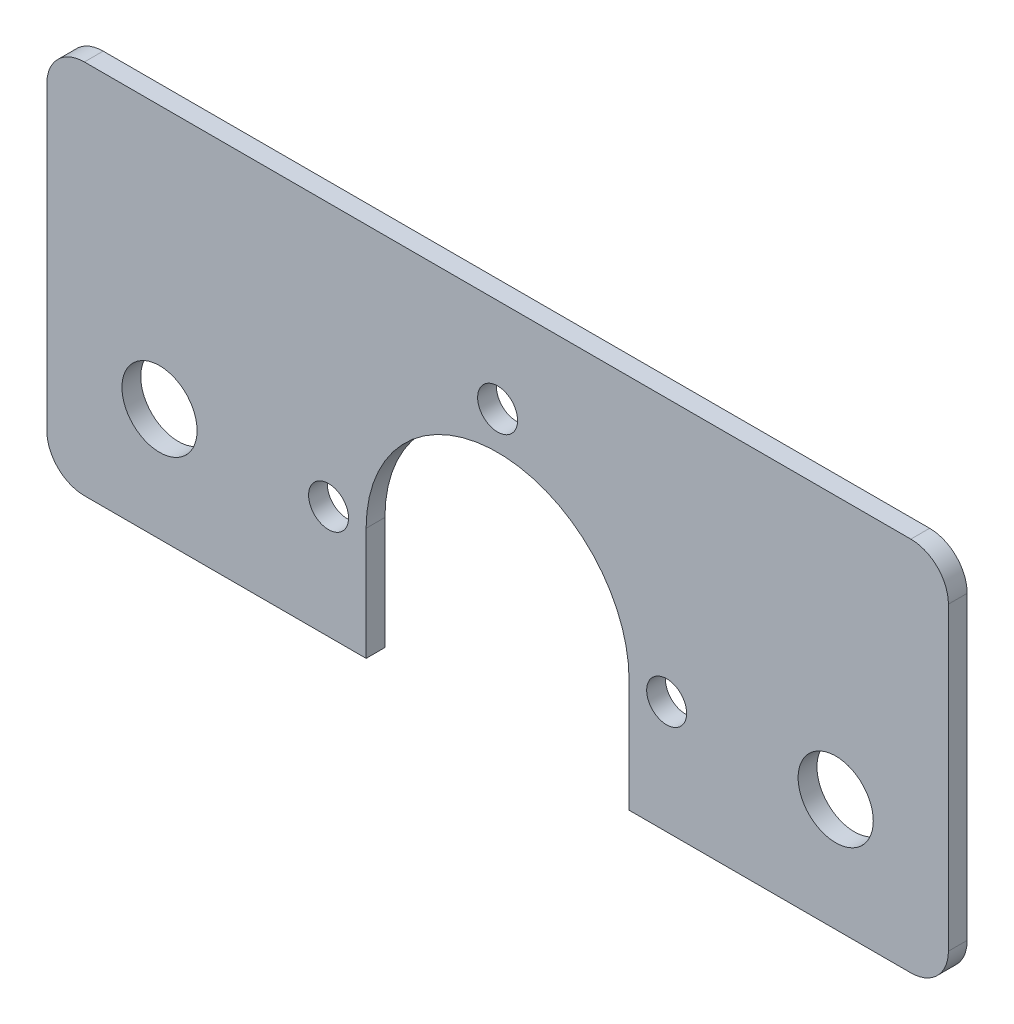
SolidWorks part; units mm, degrees
material "6061-O (SS)"
ref_plane "Front Plane" through (0, 0, 0) normal (0, 0, 1) x (1, 0, 0)
ref_plane "Top Plane" through (0, 0, 0) normal (0, 1, 0) x (1, 0, 0)
ref_plane "Right Plane" through (0, 0, 0) normal (1, 0, 0) x (0, 0, -1)
sketch "Sketch1" plane through (0, 0, 0) normal (0, 0, 1) x (1, 0, 0)
  line L0 (0, 87.7857) -> (0, -82.84) construction
  line L1 (-76.2, -44.45) -> (76.2, -44.45)
  line L2 (-76.2, -44.45) -> (-76.2, 44.45)
  line L3 (-76.2, 44.45) -> (76.2, 44.45)
  line L4 (76.2, -44.45) -> (76.2, 44.45)
  line L5 (-76.2, -44.45) -> (76.2, 44.45) construction
  line L6 (-76.2, 44.45) -> (76.2, -44.45) construction
  circle A0 centre (-28.575, 0) radius 3.3782
  circle A1 centre (0, 28.575) radius 3.3782
  circle A2 centre (28.575, 0) radius 3.3782
  circle A3 centre (0, -28.575) radius 3.3782
  circle A4 centre (-57.15, 0) radius 6.35
  circle A5 centre (57.15, 0) radius 6.35
  circle A6 centre (0, 0) radius 22.225
  point P0 (0, 0)
  point P17 (0, 0)
  dimension "D3" = 6.7564
  dimension "D4" = 12.7
  dimension "D7" = 44.45
  dimension "D2" = 28.575
  dimension "D5" = 88.9
  dimension "D6" = 152.4
  dimension "D8" = 57.15
  dimension "D1" = 4
extrude "Boss-Extrude1" add sketch "Sketch1" along normal blind 3.175 contours L1 L4 L3 L2 A0 A1 A2 A3 A4 A5
sketch "Sketch2" plane through (0, 0, 3.175) normal (0, 0, 1) x (1, 0, 0)
  line L1 (-76.2, -44.45) -> (76.2, -44.45) construction
  line L2 (-28.575, -68.58) -> (28.575, -68.58)
  line L3 (-28.575, -68.58) -> (-28.575, -20.32)
  line L4 (-28.575, -20.32) -> (28.575, -20.32)
  line L5 (28.575, -68.58) -> (28.575, -20.32)
  line L6 (-28.575, -68.58) -> (28.575, -20.32) construction
  line L7 (-28.575, -20.32) -> (28.575, -68.58) construction
  line L8 (-22.225, 0) -> (-22.225, -20.32)
  line L9 (-22.225, 0) -> (22.225, 0)
  line L10 (22.225, 0) -> (22.225, -20.32)
  circle A5 centre (0, 0) radius 22.225 construction
  point P0 (0, -44.45)
  point P13 (-28.575, 0)
  circle M5 centre (0, 0) radius 22.225
  line M6 (-76.2, -44.45) -> (76.2, -44.45)
  circle M13 centre (0, -28.575) radius 3.3782
  dimension "D1" = 20.32
extrude "Cut-Extrude1" cut sketch "Sketch2" against normal through all contours L5 L4 L3 M6 M5 M13 | L8 L4 M5 | L10 L4 M5 | L9 L4 M5 | L4 M5
sketch "Sketch3" plane through (0, 0, 3.175) normal (0, 0, 1) x (1, 0, 0)
  line L0 (76.2, -44.45) -> (76.2, 44.45) construction
  line L1 (-76.2, -44.45) -> (76.2, -44.45)
  line L2 (-76.2, -44.45) -> (-76.2, -19.05)
  line L3 (-76.2, -19.05) -> (76.2, -19.05)
  line L4 (76.2, -44.45) -> (76.2, -19.05)
  line L6 (-76.2, 44.45) -> (76.2, 44.45) construction
  dimension "D1" = 63.5
extrude "Cut-Extrude2" cut sketch "Sketch3" against normal through all
fillet "Fillet1" radius 6.35 4 edges at (76.2, -19.05, 1.5875) (76.2, 44.45, 1.5875) (-76.2, -19.05, 1.5875) (-76.2, 44.45, 1.5875)
